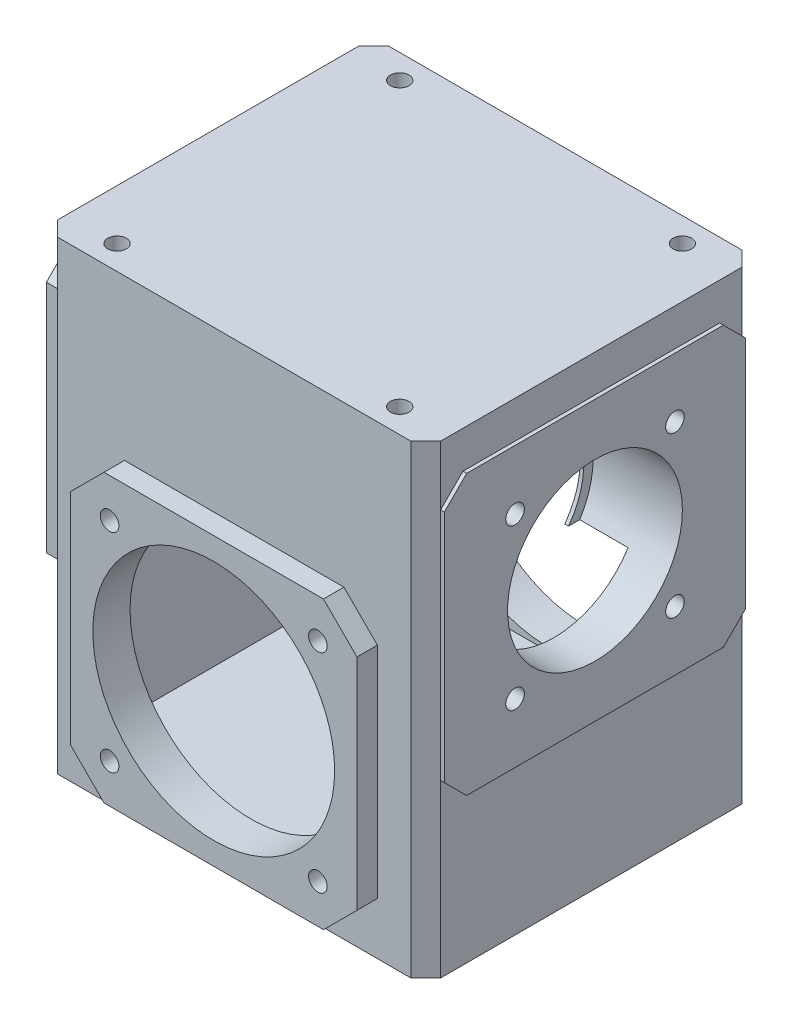
SolidWorks part; units mm, degrees
ref_plane "Front Plane" through (0, 0, 0) normal (0, 0, 1) x (1, 0, 0)
ref_plane "Top Plane" through (0, 0, 0) normal (0, 1, 0) x (1, 0, 0)
ref_plane "Right Plane" through (0, 0, 0) normal (1, 0, 0) x (0, 0, -1)
sketch "Sketch1" plane through (0, 0, 0) normal (0, 1, 0) x (1, 0, 0)
  line L0 (0, 0) -> (0, 81)
  line L1 (0, 81) -> (4, 85)
  line L2 (4, 85) -> (99, 85)
  line L3 (99, 85) -> (103, 81)
  line L4 (103, 81) -> (103, 0)
  line L5 (103, 0) -> (99, -4)
  line L6 (99, -4) -> (4, -4)
  line L7 (4, -4) -> (0, 0)
  dimension "D1" = 81
  dimension "D2" = 81
  dimension "D3" = 95
  dimension "D4" = 95
  dimension "D5" = 89
  dimension "D6" = 103
  dimension "D7" = 4
  dimension "D8" = 4
  dimension "D9" = 4
  dimension "D10" = 4
extrude "Extrude1" add sketch "Sketch1" along normal blind 125
sketch "Sketch2" plane through (0, 0, 4) normal (0, 0, 1) x (1, 0, 0)
  line L0 (4, 125) -> (99, 125) construction
  line L1 (22, 82) -> (81, 82)
  line L2 (13, 73) -> (13, 14)
  line L3 (22, 5) -> (81, 5)
  line L4 (90, 73) -> (90, 14)
  line L5 (13, 73) -> (22, 82)
  line L6 (4, 125) -> (4, 0) construction
  line L7 (81, 82) -> (90, 73)
  line L8 (13, 14) -> (22, 5)
  line L9 (81, 5) -> (90, 14)
  dimension "D2" = 59
  dimension "D3" = 43
  dimension "D4" = 9
  dimension "D5" = 9
  dimension "D6" = 59
  dimension "D10" = 59
  dimension "D11" = 59
extrude "Extrude2" add sketch "Sketch2" along normal blind 5.5
sketch "Sketch3" plane through (0, 0, -85) normal (0, 0, -1) x (-1, 0, 0)
  line L0 (-99, 125) -> (-4, 125) construction
  line L1 (-81, 82) -> (-22, 82)
  line L2 (-90, 73) -> (-90, 14)
  line L3 (-81, 5) -> (-22, 5)
  line L4 (-13, 73) -> (-13, 14)
  line L5 (-90, 73) -> (-81, 82)
  line L6 (-99, 125) -> (-99, 0) construction
  line L7 (-22, 82) -> (-13, 73)
  line L8 (-90, 14) -> (-81, 5)
  line L9 (-22, 5) -> (-13, 14)
  dimension "D2" = 59
  dimension "D3" = 9
  dimension "D4" = 43
  dimension "D5" = 9
  dimension "D6" = 59
  dimension "D7" = 9
  dimension "D8" = 9
  dimension "D9" = 9
  dimension "D10" = 59
  dimension "D11" = 59
  dimension "D12" = 77
extrude "Extrude3" add sketch "Sketch3" along normal blind 5.5
sketch "Sketch4" plane through (0, 0, 9.5) normal (0, 0, 1) x (1, 0, 0)
  line L0 (90, 14) -> (90, 73) construction
  line L1 (81, 82) -> (22, 82) construction
  circle A0 centre (51.5, 43.5) radius 32.5
  dimension "D3" = 65
  dimension "D1" = 38.5
  dimension "D2" = 38.5
extrude "Extrude5" cut sketch "Sketch4" against normal through all
sketch3d "3DSketch2" plane through (0, 0, 0) normal (0, 0, 1) x (1, 0, 0)
  dimension "D1" = 10
sketch "Sketch5" plane through (0, 0, -0.5) normal (0, 0, 1) x (1, 0, 0)
  line L0 (4, 0) -> (99, 0) construction
  line L1 (10, 10) -> (93, 10)
  line L2 (10, 10) -> (10, 65)
  line L3 (10, 65) -> (24, 65)
  line L4 (93, 10) -> (93, 65)
  line L5 (0, 125) -> (0, 0) construction
  line L6 (103, 125) -> (103, 0) construction
  line L7 (4, 125) -> (99, 125) construction
  line L9 (24, 65) -> (24, 110)
  line L10 (24, 110) -> (79, 110)
  line L11 (79, 65) -> (79, 110)
  line L12 (79, 65) -> (93, 65)
  dimension "D1" = 10
  dimension "D2" = 10
  dimension "D3" = 10
  dimension "D4" = 55
  dimension "D5" = 15
  dimension "D6" = 24
  dimension "D7" = 24
extrude "Extrude7" cut sketch "Sketch5" against normal blind 80
sketch "Sketch7" plane through (0, 0, 9.5) normal (0, 0, 1) x (1, 0, 0)
  line L0 (81, 82) -> (22, 82) construction
  line L1 (13, 73) -> (13, 14) construction
  circle A0 centre (23.5, 71.5) radius 2.5
  dimension "D3" = 5
  dimension "D1" = 10.5
  dimension "D2" = 10.5
extrude "Extrude9" cut sketch "Sketch7" against normal blind 15
pattern_linear "LPattern1" count 2 spacing 56 along (1, 0, 0) of "Extrude9"
pattern_linear "LPattern2" count 2 spacing 56 along (0, -1, 0) of "LPattern1", "Extrude9"
sketch "Sketch8" plane through (103, 0, 0) normal (1, 0, 0) x (0, 0, -1)
  line L1 (6, 115) -> (75, 115)
  line L2 (0, 109) -> (0, 46)
  line L3 (6, 40) -> (75, 40)
  line L4 (81, 109) -> (81, 46)
  line L6 (0, 125) -> (81, 125) construction
  line L7 (0, 109) -> (6, 115)
  line L8 (75, 115) -> (81, 109)
  line L9 (75, 40) -> (81, 46)
  line L10 (0, 46) -> (6, 40)
  dimension "D2" = 10
  dimension "D4" = 69
  dimension "D5" = 63
  dimension "D6" = 6
  dimension "D7" = 63
  dimension "D8" = 6
  dimension "D9" = 69
  dimension "D10" = 6
extrude "Extrude10" add sketch "Sketch8" along normal blind 1
sketch "Sketch9" plane through (0, 0, 0) normal (-1, 0, 0) x (0, 0, 1)
  line L0 (-81, 125) -> (-81, 0) construction
  line L1 (-75, 115) -> (-6, 115)
  line L2 (-81, 109) -> (-81, 46)
  line L3 (-75, 40) -> (-6, 40)
  line L4 (0, 109) -> (0, 46)
  line L5 (-81, 125) -> (0, 125) construction
  line L7 (-81, 109) -> (-75, 115)
  line L8 (-6, 115) -> (0, 109)
  line L9 (-6, 40) -> (0, 46)
  line L10 (-81, 46) -> (-75, 40)
  dimension "D2" = 0
  dimension "D3" = 85
  dimension "D4" = 69
  dimension "D5" = 63
  dimension "D6" = 6
  dimension "D7" = 63
  dimension "D8" = 6
  dimension "D9" = 69
  dimension "D10" = 6
extrude "Extrude11" add sketch "Sketch9" along normal blind 3
sketch "Sketch10" plane through (104, 0, 0) normal (1, 0, 0) x (0, 0, -1)
  line L0 (0, 109) -> (0, 46) construction
  line L1 (75, 115) -> (6, 115) construction
  circle A0 centre (40.5, 77.5) radius 23.5
  dimension "D3" = 47
  dimension "D1" = 40.5
  dimension "D2" = 37.5
extrude "Extrude12" cut sketch "Sketch10" against normal blind 24
sketch "Sketch11" plane through (80, 0, 0) normal (1, 0, 0) x (0, 0, -1)
  circle A0 centre (40.5, 77.5) radius 21
  arc A1 (60.3997, 65) -> (20.6003, 65) centre (40.5, 77.5) ccw construction
  dimension "D2" = 42
  dimension "D1" = 0
extrude "Extrude13" cut sketch "Sketch11" against normal through all
sketch "Sketch12" plane through (-3, 0, 0) normal (-1, 0, 0) x (0, 0, 1)
  circle A0 centre (-40.5, 77.5) radius 23.5
  circle A1 centre (-40.5, 77.5) radius 21 construction
  dimension "D2" = 47
  dimension "D1" = 0
  dimension "D3" = 0
extrude "Extrude14" cut sketch "Sketch12" against normal blind 24
sketch "Sketch13" plane through (104, 0, 0) normal (1, 0, 0) x (0, 0, -1)
  line L0 (75, 115) -> (6, 115) construction
  line L1 (0, 109) -> (0, 46) construction
  circle A0 centre (19, 99) radius 2.5
  dimension "D3" = 5
  dimension "D1" = 16
  dimension "D2" = 19
extrude "Extrude15" cut sketch "Sketch13" against normal blind 20
pattern_linear "LPattern3" count 2 spacing 43 along (0, 0, -1) of "Extrude15"
pattern_linear "LPattern4" count 2 spacing 43 along (0, -1, 0) of "LPattern3", "Extrude15"
sketch "Sketch14" plane through (0, 125, 0) normal (0, 1, 0) x (1, 0, 0)
  line L0 (0, 81) -> (0, 0) construction
  line L1 (99, 85) -> (4, 85) construction
  circle A0 centre (13.5, 78.5) radius 2.5
  dimension "D3" = 5
  dimension "D1" = 13.5
  dimension "D2" = 6.5
extrude "Extrude16" cut sketch "Sketch14" against normal blind 20
pattern_linear "LPattern5" count 2 spacing 76 along (1, 0, 0) of "Extrude16"
pattern_linear "LPattern6" count 2 spacing 76 along (0, 0, 1) of "LPattern5", "Extrude16"
sketch "Sketch15" plane through (0, 0, 0) normal (0, -1, 0) x (1, 0, 0)
  line L0 (0, -81) -> (0, 0) construction
  line L1 (4, 4) -> (99, 4) construction
  circle A0 centre (13.5, -2.5) radius 2.5
  dimension "D3" = 5
  dimension "D1" = 13.5
  dimension "D2" = 6.5
extrude "Extrude17" cut sketch "Sketch15" against normal blind 20
pattern_linear "LPattern7" count 2 spacing 76 along (1, 0, 0) of "Extrude17"
pattern_linear "LPattern8" count 2 spacing 76 along (0, 0, -1) of "LPattern7", "Extrude17"
sketch "Sketch16" plane through (0, 0, -90.5) normal (0, 0, -1) x (-1, 0, 0)
  line L0 (-22, 82) -> (-81, 82) construction
  line L1 (-73.5, 65.5) -> (-29.5, 65.5)
  line L2 (-73.5, 65.5) -> (-73.5, 21.5)
  line L3 (-73.5, 21.5) -> (-29.5, 21.5)
  line L4 (-29.5, 65.5) -> (-29.5, 21.5)
  line L5 (-90, 73) -> (-90, 14) construction
  dimension "D1" = 44
  dimension "D2" = 44
  dimension "D3" = 16.5
  dimension "D4" = 16.5
extrude "Extrude18" [suppressed] add sketch "Sketch16" along normal blind 3
sketch "Sketch18" plane through (0, 0, -90.5) normal (0, 0, -1) x (-1, 0, 0)
  line L0 (-90, 73) -> (-90, 14) construction
  line L1 (-22, 82) -> (-81, 82) construction
  circle A0 centre (-79.5, 71.5) radius 2.5
  dimension "D3" = 5
  dimension "D1" = 10.5
  dimension "D2" = 10.5
extrude "Extrude20" cut sketch "Sketch18" against normal blind 20
pattern_linear "LPattern9" count 2 spacing 56 along (-1, 0, 0) of "Extrude20"
pattern_linear "LPattern10" count 2 spacing 56 along (0, -1, 0) of "LPattern9", "Extrude20"
sketch "Sketch19" plane through (-3, 0, 0) normal (-1, 0, 0) x (0, 0, 1)
  line L0 (-6, 115) -> (-75, 115) construction
  line L1 (-81, 109) -> (-81, 46) construction
  circle A0 centre (-62, 99) radius 2.5
  dimension "D3" = 5
  dimension "D1" = 16
  dimension "D2" = 19
extrude "Extrude21" [suppressed] cut sketch "Sketch19" against normal blind 20
pattern_linear "LPattern11" [suppressed] count 2 spacing 43
pattern_linear "LPattern12" [suppressed] count 2 spacing 43
